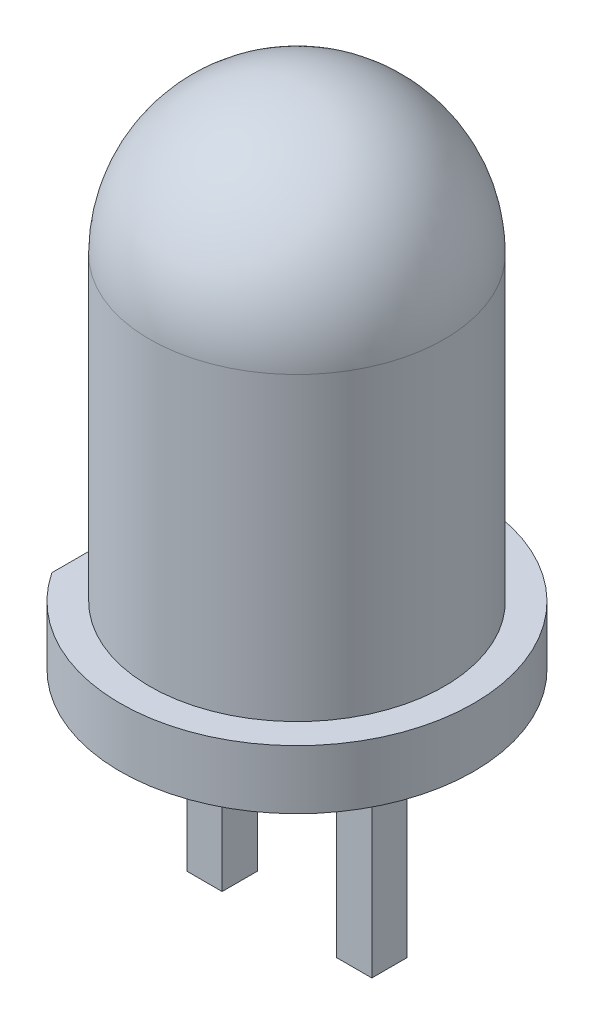
SolidWorks part; units mm, degrees
ref_plane "Plan de face" through (0, 0, 0) normal (0, 0, 1) x (1, 0, 0)
ref_plane "Plan de dessus" through (0, 0, 0) normal (0, 1, 0) x (1, 0, 0)
ref_plane "Plan de droite" through (0, 0, 0) normal (1, 0, 0) x (0, 0, -1)
sketch "Esquisse1" plane through (0, 0, 0) normal (0, 0, 1) x (1, 0, 0)
  line L0 (0, 0) -> (-3, 0)
  line L1 (-3, 0) -> (-3, 1)
  line L2 (-3, 1) -> (-2.5, 1)
  line L3 (-2.5, 1) -> (-2.5, 6.1)
  line L4 (0, 8.6) -> (0, 0)
  arc A0 (-2.5, 6.1) -> (0, 8.6) centre (0, 6.1) cw
  dimension "D1" = 2.5
  dimension "D2" = 8.6
  dimension "D3" = 3
  dimension "D4" = 1
revolve "Révolution1" add sketch "Esquisse1" angle 360 about L4
sketch "Esquisse2" plane through (0, 0, 0) normal (0, -1, 0) x (1, 0, 0)
  line L0 (-1.27, 0) -> (0, 0) construction
  line L1 (-1.57, -0.3) -> (-0.97, -0.3)
  line L2 (-1.57, -0.3) -> (-1.57, 0.3)
  line L3 (-1.57, 0.3) -> (-0.97, 0.3)
  line L4 (-0.97, -0.3) -> (-0.97, 0.3)
  line L5 (-1.57, -0.3) -> (-0.97, 0.3) construction
  line L6 (-1.57, 0.3) -> (-0.97, -0.3) construction
  line L7 (0.97, -0.3) -> (1.57, -0.3)
  line L8 (0.97, -0.3) -> (0.97, 0.3)
  line L9 (0.97, 0.3) -> (1.57, 0.3)
  line L10 (1.57, -0.3) -> (1.57, 0.3)
  line L11 (0.97, -0.3) -> (1.57, 0.3) construction
  line L12 (0.97, 0.3) -> (1.57, -0.3) construction
  line L13 (0, 0) -> (1.27, 0) construction
  point P0 (-1.27, 0)
  point P5 (1.27, 0)
  dimension "D1" = 2.54
  dimension "D2" = 0.6
extrude "Boss.-Extru.1" add sketch "Esquisse2" along normal blind 3.6
sketch "Esquisse3" plane through (0, 0, 0) normal (0, -1, 0) x (1, 0, 0)
  line L0 (-3, 0) -> (0.0527, 0) construction
  line L1 (-3.5, -2) -> (-2.5, -2)
  line L2 (-3.5, -2) -> (-3.5, 2)
  line L3 (-3.5, 2) -> (-2.5, 2)
  line L4 (-2.5, -2) -> (-2.5, 2)
  line L5 (-3.5, -2) -> (-2.5, 2) construction
  line L6 (-3.5, 2) -> (-2.5, -2) construction
  point P0 (-3, 0)
  dimension "D1" = 2.5
  dimension "D2" = 1
  dimension "D3" = 4
extrude "Enlèv. mat.-Extru.1" cut sketch "Esquisse3" against normal through all
